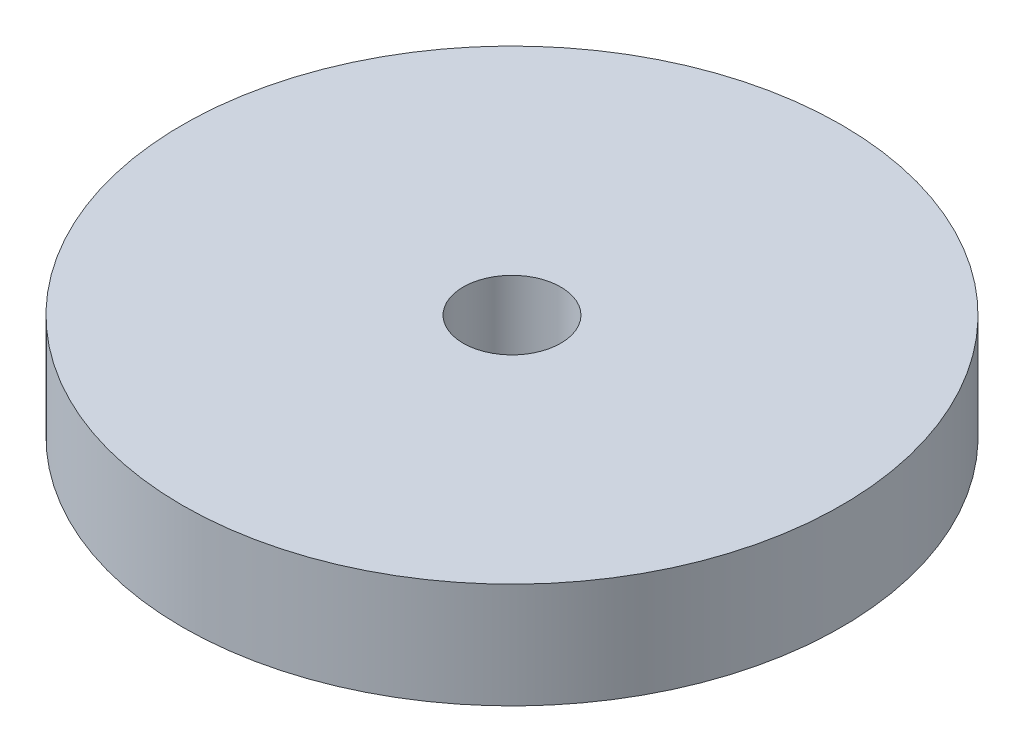
SolidWorks part; units mm, degrees
ref_plane "Front Plane" through (0, 0, 0) normal (0, 0, 1) x (1, 0, 0)
ref_plane "Top Plane" through (0, 0, 0) normal (0, 1, 0) x (1, 0, 0)
ref_plane "Right Plane" through (0, 0, 0) normal (1, 0, 0) x (0, 0, -1)
sketch "Sketch1" plane through (0, 0, 0) normal (0, 1, 0) x (1, 0, 0)
  circle A0 centre (0, 0) radius 1.85
  circle A1 centre (0, 0) radius 12.5
  dimension "D1" = 3.7
  dimension "D2" = 25
extrude "Boss-Extrude1" add sketch "Sketch1" along normal mid plane 4
